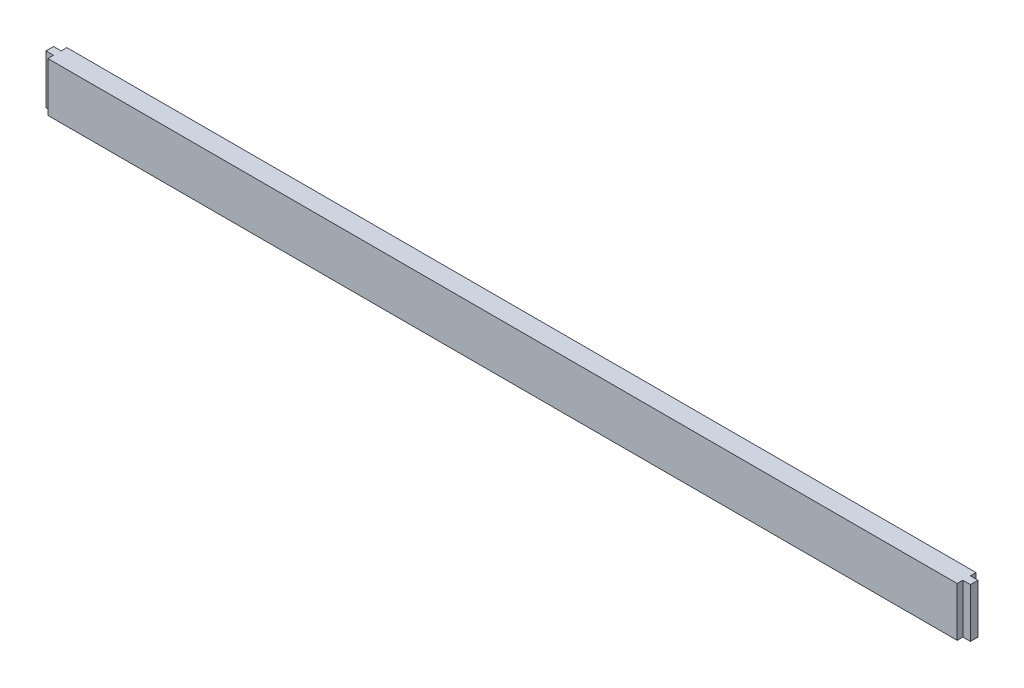
SolidWorks part; units mm, degrees
ref_plane "Front Plane" through (0, 0, 0) normal (0, 0, 1) x (1, 0, 0)
ref_plane "Top Plane" through (0, 0, 0) normal (0, 1, 0) x (1, 0, 0)
ref_plane "Right Plane" through (0, 0, 0) normal (1, 0, 0) x (0, 0, -1)
sketch "Sketch1" plane through (0, 0, 0) normal (0, 0, 1) x (1, 0, 0)
  line L1 (0, 0) -> (774.7, 0)
  line L2 (0, 0) -> (0, 41.275)
  line L3 (0, 41.275) -> (774.7, 41.275)
  line L4 (774.7, 0) -> (774.7, 41.275)
  dimension "D1" = 774.7
  dimension "D2" = 41.275
extrude "Boss-Extrude1" add sketch "Sketch1" along normal blind 15.875
sketch "Sketch2" plane through (0, 41.275, 0) normal (0, 1, 0) x (1, 0, 0)
  line L0 (-225.3, -7.9375) -> (49774.7, -7.9375) construction
  line L1 (774.7, -15.875) -> (768.35, -15.875)
  line L2 (774.7, -15.875) -> (774.7, -11.1125)
  line L3 (774.7, -11.1125) -> (768.35, -11.1125)
  line L4 (768.35, -15.875) -> (768.35, -11.1125)
  line L5 (774.7, -15.875) -> (774.7, 0) construction
  line L6 (387.35, -1019.05) -> (387.35, 48980.95) construction
  line L7 (774.7, -15.875) -> (0, -15.875) construction
  line L8 (768.35, 0) -> (768.35, -4.7625)
  line L9 (774.7, -4.7625) -> (768.35, -4.7625)
  line L10 (774.7, 0) -> (774.7, -4.7625)
  line L11 (774.7, 0) -> (768.35, 0)
  line L12 (0, 0) -> (6.35, 0)
  line L13 (0, 0) -> (0, -4.7625)
  line L14 (0, -4.7625) -> (6.35, -4.7625)
  line L15 (6.35, 0) -> (6.35, -4.7625)
  line L16 (6.35, -15.875) -> (6.35, -11.1125)
  line L17 (0, -11.1125) -> (6.35, -11.1125)
  line L18 (0, -15.875) -> (0, -11.1125)
  line L19 (0, -15.875) -> (6.35, -15.875)
  point P10 (774.7, -7.9375)
  point P15 (387.35, -15.875)
  dimension "D1" = 6.35
extrude "Cut-Extrude1" cut sketch "Sketch2" against normal through all
